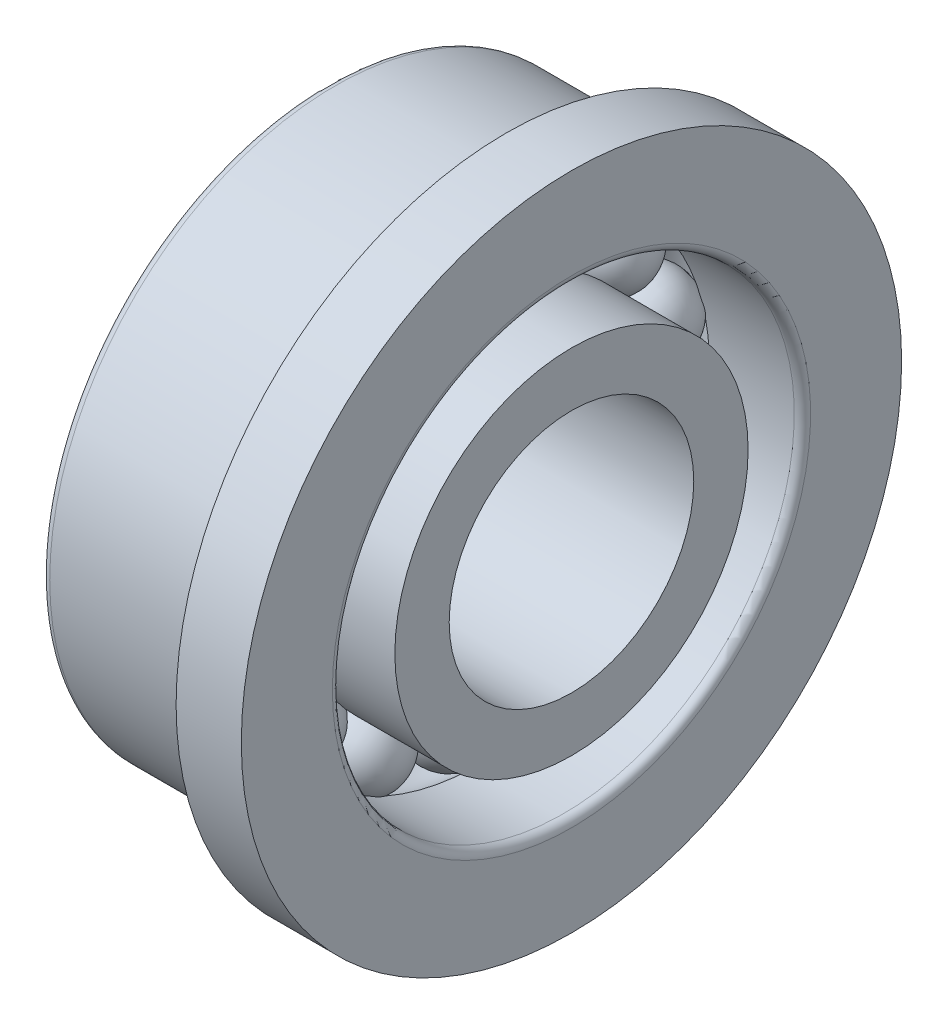
SolidWorks part; units mm, degrees
ref_plane "Front" through (0, 0, 0) normal (0, 0, 1) x (1, 0, 0)
ref_plane "Top" through (0, 0, 0) normal (0, 1, 0) x (1, 0, 0)
ref_plane "Right" through (0, 0, 0) normal (1, 0, 0) x (0, 0, -1)
sketch "Sketch1" plane through (0, 0, 0) normal (0, 0, 1) x (1, 0, 0)
  line L0 (-0.8071, 0) -> (0.9386, 0) construction
  line L1 (-0.8071, 2.5) -> (0.9386, 2.5) construction
  line L2 (-0.5, 2.5) -> (0.5, 2.5)
  arc A0 (-0.5, 2.5) -> (0.5, 2.5) centre (0, 2.5) ccw
  dimension "D2" = 1
  dimension "D1" = 2.5
revolve "Revolve1" add sketch "Sketch1" angle 360 about L1
sketch "Sketch2" plane through (0, 0, 0) normal (0, 0, 1) x (1, 0, 0)
  line L0 (-1.5, 2.1667) -> (-0.3592, 2.1667)
  line L1 (1.5, 2.1667) -> (1.5, 1.5)
  line L2 (1.5, 1.5) -> (-1.5, 1.5)
  line L3 (-1.5, 1.5) -> (-1.5, 2.1667)
  line L4 (-0.8417, 0) -> (1.1297, 0) construction
  line L5 (-0.8417, 2.5) -> (0.9121, 2.5) construction
  line L6 (0.3592, 2.1667) -> (1.5, 2.1667)
  arc A0 (-0.3592, 2.1667) -> (0.3592, 2.1667) centre (0, 2.5) ccw
  dimension "D6" = 0.98
  dimension "D1" = 3
  dimension "D2" = 2.5
  dimension "D3" = 3
  dimension "D4" = 1.5
  dimension "D5" = 4.3333
revolve "Revolve2" add sketch "Sketch2" angle 360 about L4
sketch "Sketch3" plane through (0, 0, 0) normal (0, 0, 1) x (1, 0, 0)
  line L0 (-1.5, 3.5) -> (-1.5, 2.8333)
  line L1 (-1.5, 2.8333) -> (-0.3592, 2.8333)
  line L2 (1.5, 2.8333) -> (1.5, 4.05)
  line L3 (1.5, 4.05) -> (0.7, 4.05)
  line L4 (0.7, 4.05) -> (0.7, 3.5275)
  line L5 (0.6725, 3.5) -> (-1.5, 3.5)
  line L6 (-0.9997, 0) -> (1.1297, 0) construction
  line L8 (-0.9997, 2.5) -> (0.9355, 2.5) construction
  line L9 (0.3592, 2.8333) -> (1.5, 2.8333)
  arc A0 (0.3592, 2.8333) -> (-0.3592, 2.8333) centre (0, 2.5) ccw
  arc A1 (0.6725, 3.5) -> (0.7, 3.5275) centre (0.7, 3.5) ccw
  dimension "D8" = 0.98
  dimension "D1" = 0.055
  dimension "R" = 2.5
  dimension "DD" = 7
  dimension "DD1" = 8.1
  dimension "C1" = 0.8
  dimension "B" = 3
  dimension "D6" = 1.5
  dimension "D7" = 5.6667
revolve "Revolve3" add sketch "Sketch3" angle 360 about L6
pattern_circular "Circular-Pattern1" count 14 over 360 about axis through (0, 0, 0) along (1, 0, 0) of "Revolve1"
fillet "Fillet1" radius 0.1 3 edges at (1.5, 0, 2.8333) (-1.5, 0, 3.5) (-1.5, 0, 1.5)
equation "\"D1@Sketch1\" = ( \"DD@Sketch3\" + \"D1@Sketch2\" )  / 4"
equation "\"D2@Sketch1\" =  ( \"DD@Sketch3\" - \"D1@Sketch2\" )  / 4"
equation "\"D4@Sketch2\" = \"D3@Sketch2\" / 2"
equation "\"D5@Sketch2\" = \"D1@Sketch2\" +  ( \"DD@Sketch3\" - \"D1@Sketch2\" )  / 3"
equation "\"D2@Sketch2\" = ( \"DD@Sketch3\" + \"D1@Sketch2\" )  / 4"
equation "\"D6@Sketch2\" =  ( \"DD@Sketch3\" - \"D1@Sketch2\" )  / 4 - 0.02"
equation "\"B@Sketch3\" = \"D3@Sketch2\""
equation "\"D6@Sketch3\" = \"B@Sketch3\" / 2"
equation "\"R@Sketch3\" = ( \"DD@Sketch3\" + \"D1@Sketch2\" )  / 4"
equation "\"D7@Sketch3\" = \"DD@Sketch3\" -  ( \"DD@Sketch3\"  - \"D1@Sketch2\") / 3 "
equation "\"D8@Sketch3\" = ( \"DD@Sketch3\" - \"D1@Sketch2\" )  / 4 - 0.02"
equation "\"m@Circular-Pattern1\" = int( 3.14159265 / atn((\"D2@Sketch1\"/2) / sqr(( \"DD@Sketch3\" + \"D1@Sketch2\" )  / 4 * ( \"DD@Sketch3\" + \"D1@Sketch2\" )  / 4 - (\"D2@Sketch1\"/2) *  (\"D2@Sketch1\"/2))))-1"
equation "\"D1@Sketch3\" =  ( \"DD1@Sketch3\" - \"DD@Sketch3\" )  / 20"
